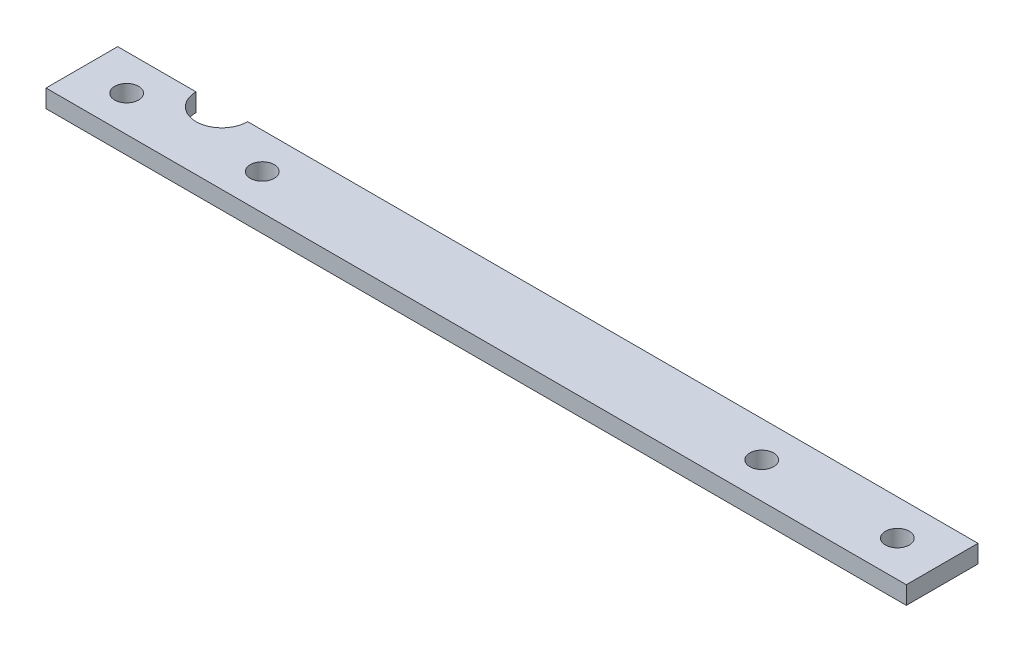
SolidWorks part; units mm, degrees
ref_plane "Front Plane" through (0, 0, 0) normal (0, 0, 1) x (1, 0, 0)
ref_plane "Top Plane" through (0, 0, 0) normal (0, 1, 0) x (1, 0, 0)
ref_plane "Right Plane" through (0, 0, 0) normal (1, 0, 0) x (0, 0, -1)
sketch "Sketch1" plane through (0, 0, 0) normal (0, 1, 0) x (1, 0, 0)
  line L1 (-114.3, 9.525) -> (114.3, 9.525)
  line L2 (-114.3, 9.525) -> (-114.3, -9.525)
  line L3 (-114.3, -9.525) -> (114.3, -9.525)
  line L4 (114.3, 9.525) -> (114.3, -9.525)
  line L5 (-114.3, 9.525) -> (114.3, -9.525) construction
  line L6 (-114.3, -9.525) -> (114.3, 9.525) construction
  point P0 (0, 0)
  dimension "D1" = 228.6
  dimension "D2" = 19.05
extrude "Boss-Extrude1" add sketch "Sketch1" along normal blind 4.7625 contours L1 L4 L3 L2
sketch "Sketch2" plane through (0, 4.7625, 0) normal (0, 1, 0) x (1, 0, 0)
  line L0 (114.3, 9.525) -> (114.3, -9.525) construction
  line L1 (0, 0) -> (0, 42.976) construction
  circle A0 centre (102.3937, 0) radius 3.175
  circle A1 centre (-102.3937, 0) radius 3.175
  point P2 (114.3, 0)
  dimension "D1" = 6.35
  dimension "D2" = 11.9062
extrude "Cut-Extrude1" cut sketch "Sketch2" against normal through all
sketch "Sketch3" plane through (0, 4.7625, 0) normal (0, 1, 0) x (1, 0, 0)
  line L0 (-114.3, 9.525) -> (114.3, 9.525) construction
  line L1 (-114.3, 9.525) -> (-114.3, -9.525) construction
  circle A0 centre (-86.614, 9.525) radius 6.858
  dimension "D1" = 13.716
  dimension "D2" = 27.686
extrude "Cut-Extrude2" cut sketch "Sketch3" against normal through all
sketch "Sketch4" plane through (0, 4.7625, 0) normal (0, 1, 0) x (1, 0, 0)
  line L0 (0, 0) -> (-78.9042, 0) construction
  circle A0 centre (-66.3575, 0) radius 3.175
  circle A1 centre (66.3575, 0) radius 3.175
  dimension "D1" = 6.35
  dimension "D2" = 66.3575
  dimension "D3" = 66.3575
extrude "Cut-Extrude3" cut sketch "Sketch4" against normal through all
